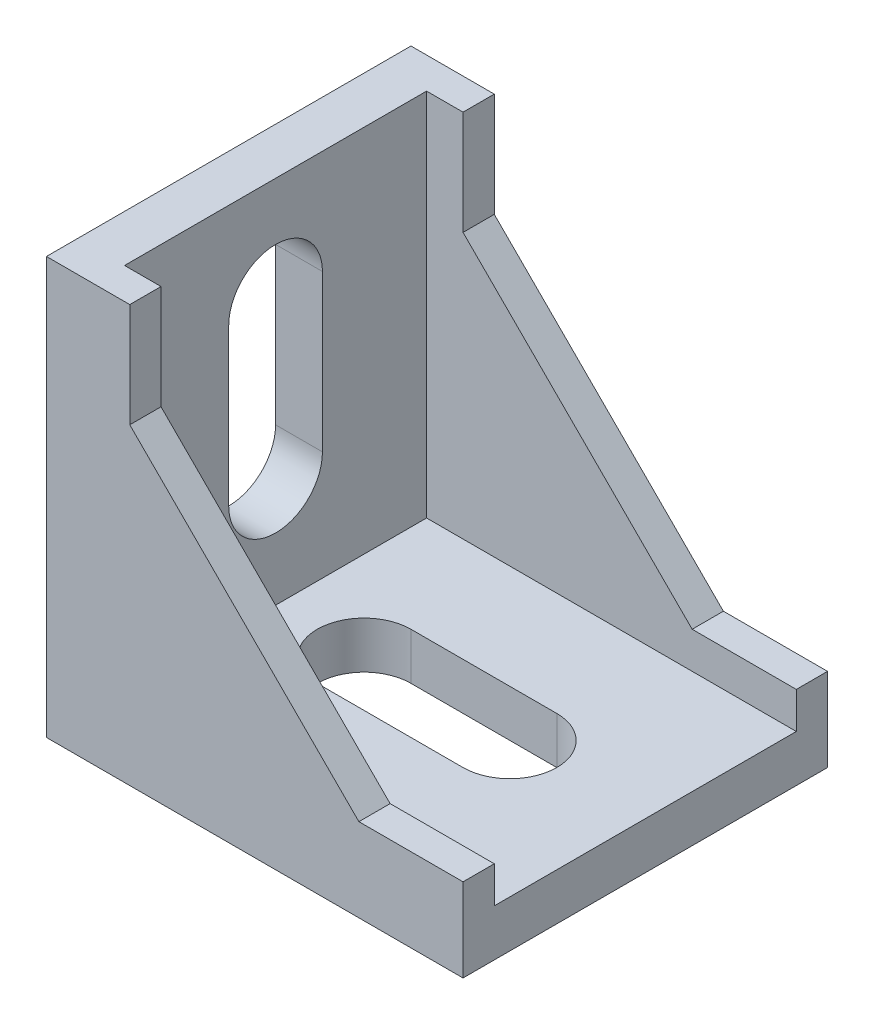
SolidWorks part; units mm, degrees
ref_plane "前视" through (0, 0, 0) normal (0, 0, 1) x (1, 0, 0)
ref_plane "上视" through (0, 0, 0) normal (0, 1, 0) x (1, 0, 0)
ref_plane "右视" through (0, 0, 0) normal (1, 0, 0) x (0, 0, -1)
sketch "草图1" plane through (0, 0, 0) normal (0, 0, 1) x (1, 0, 0)
  line L0 (0, 40) -> (0, 0)
  line L1 (0, 0) -> (40, 0)
  line L2 (0, 40) -> (8, 40)
  line L4 (40, 8) -> (40, 0)
  line L5 (8, 40) -> (8, 30)
  line L6 (8, 30) -> (30, 8)
  line L7 (30, 8) -> (40, 8)
  dimension "D1" = 40
  dimension "D2" = 40
  dimension "D3" = 10
  dimension "D4" = 10
  dimension "D5" = 8
  dimension "D6" = 8
extrude "凸台-拉伸1" add sketch "草图1" against normal mid plane 35
sketch "草图2" plane through (0, 0, 0) normal (0, 0, 1) x (1, 0, 0)
  line L0 (4.5, 40) -> (4.5, 4.5)
  line L1 (8, 40) -> (0, 40) construction
  line L2 (4.5, 4.5) -> (40, 4.5)
  line L3 (40, 0) -> (40, 8) construction
  line L4 (40, 4.5) -> (40, 8)
  line L5 (40, 8) -> (8, 40)
  line L6 (8, 40) -> (4.5, 40)
  line L7 (0, 40) -> (0, 0) construction
  line L8 (0, 0) -> (40, 0) construction
  dimension "D1" = 4.5
  dimension "D2" = 4.5
extrude "切除-拉伸1" cut sketch "草图2" against normal mid plane 29
sketch "草图3" plane through (0, 0, 0) normal (0, -1, 0) x (1, 0, 0)
  line L0 (0, 0) -> (4.0987, 0) construction
  line L1 (13, 0) -> (27, 0) construction
  line L2 (13, -4.5) -> (27, -4.5)
  line L3 (13, 4.5) -> (27, 4.5)
  line L4 (40, -17.5) -> (40, 17.5) construction
  line L5 (0, -17.5) -> (0, 17.5) construction
  arc A0 (13, -4.5) -> (13, 4.5) centre (13, 0) cw
  arc A1 (27, -4.5) -> (27, 4.5) centre (27, 0) ccw
  dimension "D3" = 8.5
  dimension "D4" = 8.5
  dimension "D5" = 14
  dimension "D1" = 4.5
  dimension "D2" = 4.5
extrude "切除-拉伸2" cut sketch "草图3" against normal up to next
sketch "草图4" plane through (0, 0, 0) normal (-1, 0, 0) x (0, 0, 1)
  line L0 (0, 0) -> (0, -5.3778) construction
  line L1 (0, 15) -> (0, 30) construction
  line L2 (4.5, 15) -> (4.5, 30)
  line L3 (-4.5, 15) -> (-4.5, 30)
  line L4 (-17.5, 40) -> (17.5, 40) construction
  line L5 (-17.5, 0) -> (17.5, 0) construction
  arc A0 (4.5, 15) -> (-4.5, 15) centre (0, 15) cw
  arc A1 (4.5, 30) -> (-4.5, 30) centre (0, 30) ccw
  dimension "D3" = 10
  dimension "D4" = 15
  dimension "D5" = 15
  dimension "D1" = 4.5
  dimension "D2" = 4.5
extrude "切除-拉伸3" cut sketch "草图4" against normal up to next
